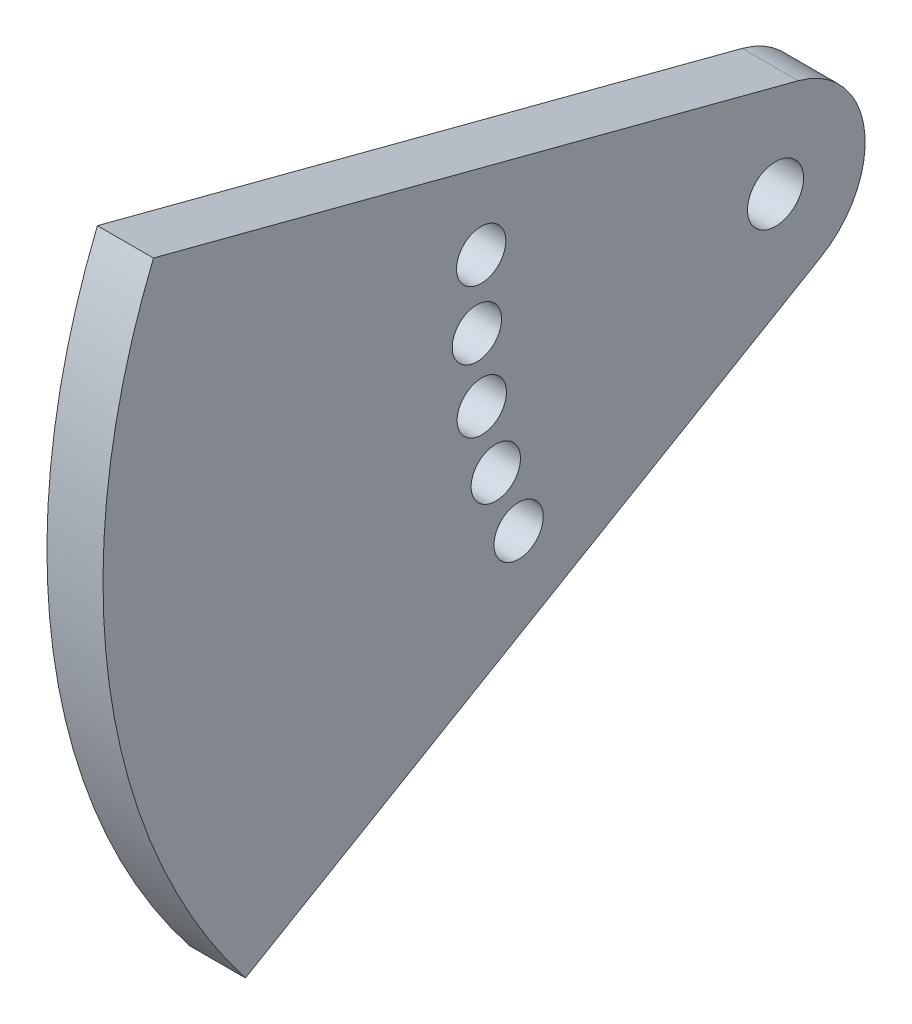
SolidWorks part; units mm, degrees
ref_plane "Front" through (0, 0, 0) normal (0, 0, 1) x (1, 0, 0)
ref_plane "Top" through (0, 0, 0) normal (0, 1, 0) x (1, 0, 0)
ref_plane "Right" through (0, 0, 0) normal (1, 0, 0) x (0, 0, -1)
sketch "Sketch1" plane through (0, 0, 0) normal (1, 0, 0) x (0, 0, -1)
  line L0 (2.5739, 9.8286) -> (-70.4822, 28.9604)
  line L1 (5.1298, -8.7699) -> (-60.0568, -46.9001)
  line L2 (19.6759, 3.5027) -> (-33.3472, 10.7) construction
  line L3 (19.6759, 3.5027) -> (-33.8328, 3.2506) construction
  arc A0 (-60.0568, -46.9001) -> (-70.4822, 28.9604) centre (0, 0) cw
  arc A1 (2.5739, 9.8286) -> (5.1298, -8.7699) centre (0, 0) cw
  circle A2 centre (-33.3472, 10.7) radius 2.794
  arc A3 (-23.8, -25.6921) -> (-29.8484, 18.3193) centre (0, 0) cw construction
  circle A4 centre (-33.8328, 3.2506) radius 2.794
  circle A5 centre (-33.277, -4.1939) radius 2.794
  circle A6 centre (-31.6905, -11.4887) radius 2.794
  circle A7 centre (-29.1042, -18.4916) radius 2.794
  circle A8 centre (0, 0) radius 3.175
  dimension "D4" = 10.16
  dimension "D6" = 5.588
  dimension "D11" = 7.4652
  dimension "D13" = 6.35
  dimension "D1" = 45
  dimension "D2" = 76.2
  dimension "D3" = 76.2
  dimension "D5" = 65.1867
  dimension "D8" = 8
  dimension "D9" = 8.2571
  dimension "D10" = 8.9432
  dimension "D12" = 7.2947
  dimension "D7" = 5
extrude "Boss-Extrude1" add sketch "Sketch1" along normal blind 6.35 contours A1 L0 A0 L1 A7 A6 A5 A4 A2
